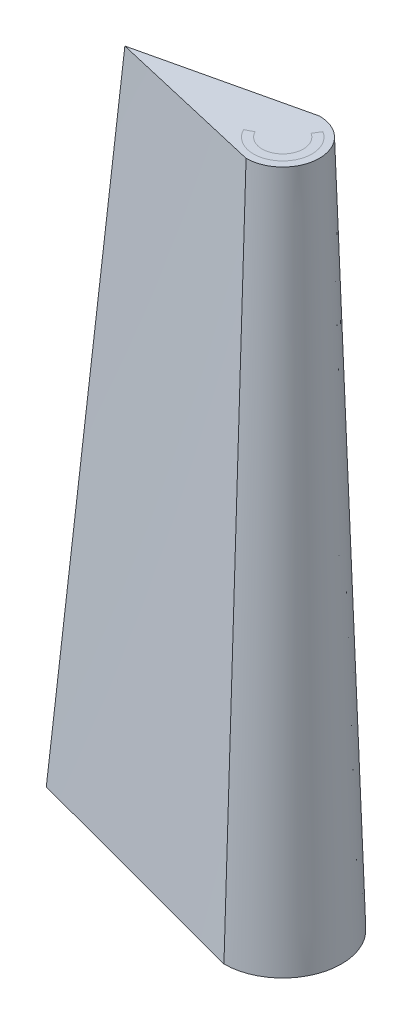
SolidWorks part; units mm, degrees
ref_plane "Front Plane" through (0, 0, 0) normal (0, 0, 1) x (1, 0, 0)
ref_plane "Top Plane" through (0, 0, 0) normal (0, 1, 0) x (1, 0, 0)
ref_plane "Right Plane" through (0, 0, 0) normal (1, 0, 0) x (0, 0, -1)
sketch "Sketch1" plane through (0, 0, 0) normal (0, 0, 1) x (1, 0, 0)
  line L0 (0, 2.9318) -> (0, -2.9639) construction
  line L1 (-0.762, 2.825) -> (-1.4804, -22.575)
  line L2 (-1.0796, 2.825) -> (-1.798, -22.575)
  line L3 (-1.0796, 2.825) -> (-0.762, 2.825)
  line L4 (-1.4804, -22.575) -> (-1.798, -22.575)
  dimension "D1" = 0.3175
  dimension "D2" = 0.762
  dimension "D3" = 25.4
revolve "Revolve1" add sketch "Sketch1" angle 360 about L0
sketch "Sketch2" plane through (0, -22.575, 0) normal (0, -1, 0) x (1, 0, 0)
  line L1 (-8.9611, -0.2152) -> (0, 2.1747)
  line L2 (-8.9611, -0.2152) -> (0, -2.1747)
  arc A0 (0, -2.1747) -> (0, 2.1747) centre (0, 0) ccw
  point P5 (-12.3518, 0)
  point P6 (-8.9611, -0.2152)
sketch "Sketch3" plane through (0, 2.825, 0) normal (0, 1, 0) x (1, 0, 0)
  line L1 (-5.839, 0) -> (0, 1.3558)
  line L2 (-5.839, 0) -> (0, -1.3558)
  arc A0 (0, -1.3558) -> (0, 1.3558) centre (0, 0) ccw
  point P5 (-5.839, 0)
loft "Loft1" add profiles "Sketch2", "Sketch3"
